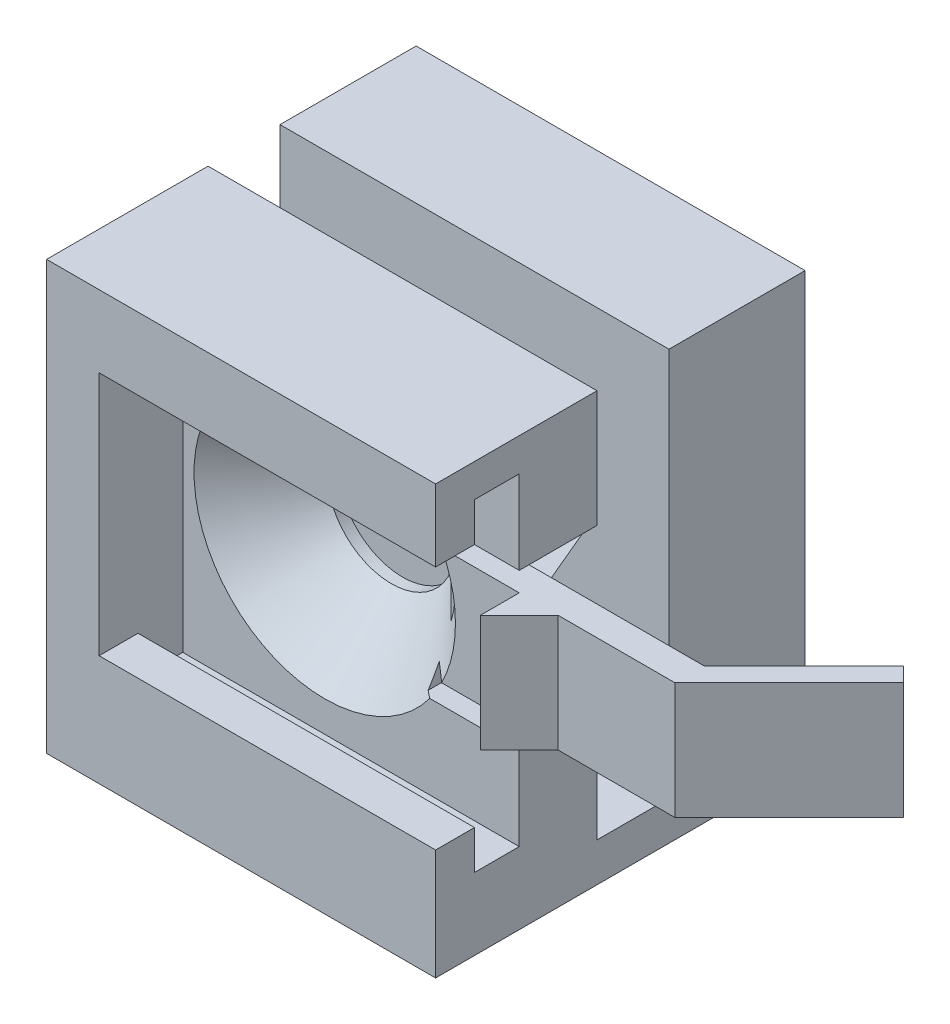
SolidWorks part; units mm, degrees
ref_plane "Alzado" through (0, 0, 0) normal (0, 0, 1) x (1, 0, 0)
ref_plane "Planta" through (0, 0, 0) normal (0, 1, 0) x (1, 0, 0)
ref_plane "Vista lateral" through (0, 0, 0) normal (1, 0, 0) x (0, 0, -1)
sketch "Croquis1" plane through (0, 0, 0) normal (0, 0, 1) x (1, 0, 0)
  line L1 (-10, -10) -> (10, -10)
  line L2 (-10, -10) -> (-10, 10)
  line L3 (-10, 10) -> (10, 10)
  line L4 (10, -10) -> (10, 10)
  line L5 (-10, -10) -> (10, 10) construction
  line L6 (-10, 10) -> (10, -10) construction
  circle A0 centre (0, 0) radius 3.1
  point P0 (0, 0)
  dimension "D3" = 6.2
  dimension "D1" = 20
  dimension "D2" = 20
extrude "Saliente-Extruir1" add sketch "Croquis1" along normal blind 4
sketch "Croquis3" plane through (0, 0, 4) normal (0, 0, 1) x (1, 0, 0)
  line L0 (10, 10) -> (-10, 10)
  line L1 (-10, 10) -> (-10, -10)
  line L2 (-10, -10) -> (10, -10)
  line L3 (10, -10) -> (10, -8.3)
  line L4 (10, -10) -> (10, 10) construction
  line L5 (10, -8.3) -> (-7.3, -8.3)
  line L6 (-7.3, -8.3) -> (-7.3, 8.3)
  line L7 (-7.3, 8.3) -> (10, 8.3)
  line L8 (10, 8.3) -> (10, 10)
  dimension "D1" = 16.6
  dimension "D2" = 1.7
  dimension "D3" = 17.3
extrude "Saliente-Extruir2" add sketch "Croquis3" along normal blind 2.3
sketch "Croquis6" plane through (0, 0, 6.3) normal (0, 0, 1) x (1, 0, 0)
  line L0 (10, 10) -> (10, 6.3)
  line L1 (10, -8.3) -> (10, 8.3) construction
  line L2 (10, 6.3) -> (-7.3, 6.3)
  line L3 (-7.3, -8.3) -> (-7.3, 8.3) construction
  line L4 (-7.3, 6.3) -> (-7.3, -6.3)
  line L5 (-7.3, -6.3) -> (10, -6.3)
  line L6 (10, -6.3) -> (10, -10)
  line L7 (10, -10) -> (-10, -10)
  line L8 (-10, -10) -> (-10, 10)
  line L9 (-10, 10) -> (10, 10)
  line L10 (10, -8.3) -> (-7.3, -8.3) construction
  line L11 (-7.3, 8.3) -> (10, 8.3) construction
  dimension "D1" = 2
  dimension "D2" = 2
extrude "Saliente-Extruir4" add sketch "Croquis6" along normal blind 2
sketch "Croquis7" plane through (0, 0, 4) normal (0, 0, 1) x (1, 0, 0)
  line L0 (10, 0) -> (10, 3)
  line L1 (10, -8.3) -> (10, 8.3) construction
  line L2 (10, 3) -> (18, 3)
  line L3 (18, 3) -> (18, 0)
  line L4 (10, 0) -> (18, 0) construction
  line L5 (18, -3) -> (18, 0)
  line L6 (10, -3) -> (18, -3)
  line L7 (10, 0) -> (10, -3)
  dimension "D1" = 3
  dimension "D2" = 8
extrude "Saliente-Extruir5" add sketch "Croquis7" against normal up to vertex (4 mm away) up to point (10, 10, 0)
sketch "Croquis9" plane through (0, -3, 0) normal (0, -1, 0) x (1, 0, 0)
  line L0 (12, 4) -> (10, 6)
  line L1 (10, 8.3) -> (10, 0) construction
  line L2 (10, 6) -> (10, 4)
  line L3 (10, 4) -> (12, 4)
  dimension "D1" = 2
  dimension "D2" = 2
extrude "Saliente-Extruir6" add sketch "Croquis9" against normal up to vertex
sketch "Croquis10" plane through (0, 0, 4) normal (0, 0, 1) x (1, 0, 0)
  line L0 (10, 3) -> (5, 3)
  line L2 (5, -3) -> (10, -3)
  line L3 (10, -3) -> (10, -4)
  line L4 (10, -8.3) -> (10, -3) construction
  line L5 (10, -4) -> (5, -4)
  line L7 (5, 4) -> (10, 4)
  line L8 (10, 3) -> (10, 8.3) construction
  line L9 (10, 4) -> (10, 3)
  line L10 (5, 4) -> (5, 3)
  line L11 (5, -3) -> (5, -4)
  line L12 (10, 3) -> (10, -3) construction
  dimension "D1" = 1
  dimension "D2" = 1
  dimension "D3" = 5
  dimension "D4" = 5
extrude "Cortar-Extruir2" cut sketch "Croquis10" against normal up to vertex (4 mm away)
sketch "Croquis11" plane through (18, 0, 0) normal (1, 0, 0) x (0, 0, -1)
  line L1 (-2.5, -3) -> (0, -3)
  line L2 (-2.5, -3) -> (-2.5, 3)
  line L3 (-2.5, 3) -> (0, 3)
  line L4 (0, -3) -> (0, 3)
  line L6 (-4, -3) -> (-4, 3) construction
  point P5 (3, 3)
  point P6 (0, 3)
  point P7 (0, -3)
  dimension "D1" = 1.5
extrude "Cortar-Extruir3" cut sketch "Croquis11" against normal up to vertex
sketch "Croquis12" plane through (0, 3, 0) normal (0, 1, 0) x (1, 0, 0)
  line L0 (18, -2.5) -> (23.1259, 2.6259)
  line L1 (23.1259, 2.6259) -> (23.8759, 1.8759)
  line L2 (18, -4) -> (23.8759, 1.8759)
  line L3 (18, -4) -> (18, -2.5)
  line L4 (12, -4) -> (10, -6) construction
  point P4 (18, -4)
  point P8 (18, -1.5)
  point P10 (23.2145, 3.7264)
  dimension "D1" = 7.2492
extrude "Saliente-Extruir7" add sketch "Croquis12" against normal up to vertex
hole_wizard "Refrentado para tornillo tapón con cabeza plana de clavija de M61" positions "Croquis3D1" profile "Croquis13" countersink size "M6" standard "Ansi Metric" end condition through all
sketch3d "Croquis3D1"
  line L0 (0, 0, 4) -> (0, 0, 0) construction
  point P0 (0, 0, 4)
sketch "Croquis13" plane through (0, 0, 4) normal (1, 0, 0) x (0, -1, 0)
  line L0 (0, 0) -> (0, 6.6259)
  line L1 (0, 6.6259) -> (3.3, 6.6259)
  line L2 (3.3, 6.6259) -> (3.3, 3.42)
  line L3 (3.3, 3.42) -> (6.72, 0)
  line L5 (6.72, 0) -> (0, 0)
  line L6 (-3.3, 3.42) -> (-6.72, 0) construction
  line L11 (0, -6.35) -> (0, 107.95) construction
  dimension "Diámetro de taladro hasta el siguiente" = 6.6
  dimension "Profundidad de taladro hasta el siguiente" = 6.6259
  dimension "Diámetro de avellanado cercano" = 13.44
  dimension "Ángulo de avellanado cercano" = 90
sketch "Croquis14" plane through (0, -10, 0) normal (0, -1, 0) x (1, 0, 0)
  line L6 (-10, 8.3) -> (10, 8.3)
  line L7 (-10, 8.3) -> (-10, -10.7)
  line L8 (-10, -10.7) -> (10, -10.7)
  line L9 (10, 8.3) -> (10, -10.7)
  dimension "D1" = 19
extrude "Saliente-Extruir8" add sketch "Croquis14" along normal blind 2
sketch "Croquis15" plane through (0, -10, 0) normal (0, 1, 0) x (1, 0, 0)
  line L0 (-10, 0) -> (-10, 10.7) construction
  line L1 (10, 10.7) -> (-10, 10.7)
  line L2 (10, 10.7) -> (10, 3.7)
  line L3 (10, 3.7) -> (-10, 3.7)
  line L4 (-10, 10.7) -> (-10, 3.7)
  dimension "D1" = 7
extrude "Saliente-Extruir9" add sketch "Croquis15" along normal up to vertex (20 mm away) up to point (-10, 10, 0)
sketch "Croquis16" plane through (0, 0, -3.7) normal (0, 0, 1) x (1, 0, 0)
  line L1 (5.8024, 0) -> (2.9012, 5.025)
  line L2 (2.9012, 5.025) -> (-2.9012, 5.025)
  line L3 (-2.9012, 5.025) -> (-5.8024, 0)
  line L4 (-5.8024, 0) -> (-2.9012, -5.025)
  line L5 (-2.9012, -5.025) -> (2.9012, -5.025)
  line L6 (2.9012, -5.025) -> (5.8024, 0)
  circle A0 centre (0, 0) radius 5.025 construction
  dimension "D1" = 10.05
extrude "Cortar-Extruir4" cut sketch "Croquis16" against normal blind 5
sketch "Croquis17" plane through (0, 0, -8.7) normal (0, 0, 1) x (1, 0, 0)
  circle A0 centre (0, 0) radius 3.3
extrude "Cortar-Extruir5" cut sketch "Croquis17" against normal up to vertex (2 mm away)
sketch "Croquis19" plane through (0, -3, 0) normal (0, -1, 0) x (1, 0, 0)
  line L0 (5, 2.5) -> (7, 2.5)
  line L1 (5, 2.5) -> (18, 2.5) construction
  line L2 (7, 2.5) -> (5, 0)
  line L3 (5, 0) -> (5, 2.5)
  point P6 (5, 0)
  dimension "D1" = 2
extrude "Saliente-Extruir10" add sketch "Croquis19" against normal up to vertex
